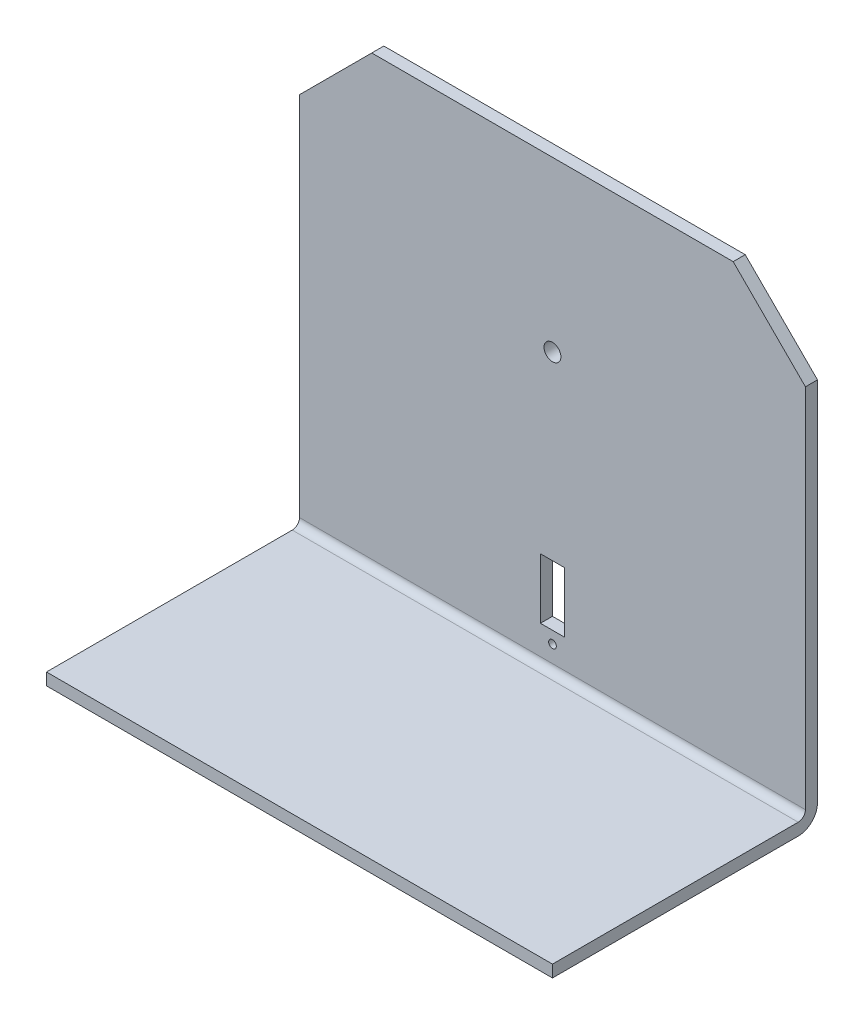
SolidWorks part; units mm, degrees
ref_plane "Front Plane" through (0, 0, 0) normal (0, 0, 1) x (1, 0, 0)
ref_plane "Top Plane" through (0, 0, 0) normal (0, 1, 0) x (1, 0, 0)
ref_plane "Right Plane" through (0, 0, 0) normal (1, 0, 0) x (0, 0, -1)
sketch "Sketch1" plane through (0, 0, 0) normal (1, 0, 0) x (0, 0, -1)
  line L0 (0, 190) -> (0, 0)
  line L1 (0, 0) -> (-110, 0)
  line L2 (-110, 0) -> (-110, 5)
  line L3 (-110, 5) -> (-5, 5)
  line L4 (-5, 5) -> (-5, 190)
  line L5 (-5, 190) -> (0, 190)
  dimension "D1" = 5
  dimension "D2" = 5
  dimension "D3" = 190
  dimension "D4" = 110
extrude "Boss-Extrude1" add sketch "Sketch1" along normal blind 210
fillet "Fillet1" radius 3 1 edges at (105, 5, 5)
fillet "Fillet2" radius 8 1 edges at (105, 0, 0)
sketch "Sketch2" plane through (0, 0, 0) normal (0, 0, -1) x (-1, 0, 0)
  line L0 (-105, 190) -> (-105, 0) construction
  line L1 (-210, 190) -> (0, 190) construction
  line L2 (0, 0) -> (-210, 0) construction
  line L4 (-110, 20) -> (-100, 20)
  line L5 (-110, 20) -> (-110, 45)
  line L6 (-110, 45) -> (-100, 45)
  line L7 (-100, 20) -> (-100, 45)
  line L8 (-110, 20) -> (-100, 45) construction
  line L9 (-110, 45) -> (-100, 20) construction
  circle A0 centre (-105, 120) radius 3.5
  circle A1 centre (-105, 15) radius 1.6
  point P8 (-105, 32.5)
  dimension "D1" = 7
  dimension "D2" = 70
  dimension "D6" = 3.2
  dimension "D3" = 45
  dimension "D4" = 20
  dimension "D5" = 10
  dimension "D7" = 15
extrude "Cut-Extrude1" cut sketch "Sketch2" against normal through all
chamfer "Chamfer1" distance 30 angle 45 2 edges at (0, 190, 2.5) (210, 190, 2.5)
